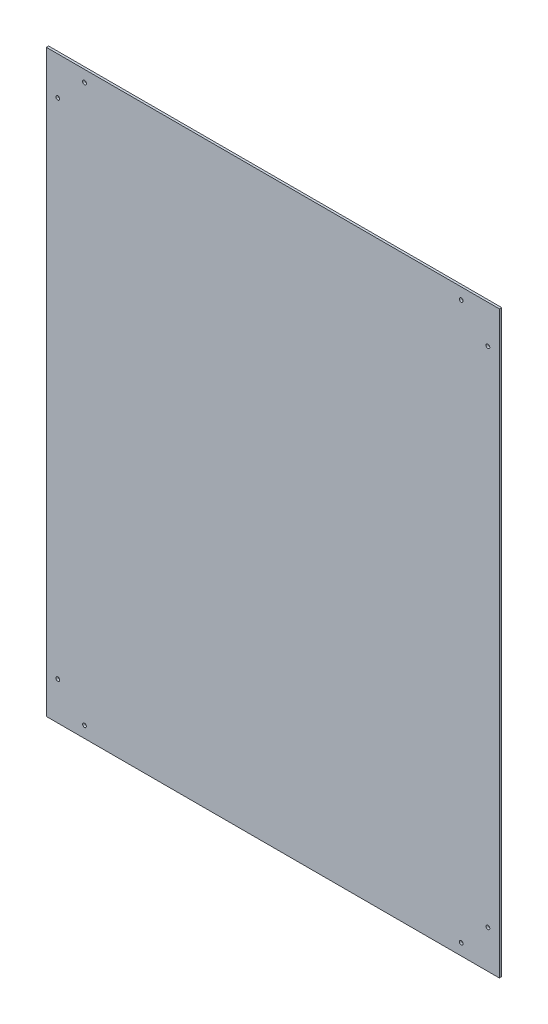
SolidWorks part; units mm, degrees
ref_plane "Plan de face" through (0, 0, 0) normal (0, 0, 1) x (1, 0, 0)
ref_plane "Plan de dessus" through (0, 0, 0) normal (0, 1, 0) x (1, 0, 0)
ref_plane "Plan de droite" through (0, 0, 0) normal (1, 0, 0) x (0, 0, -1)
sketch "Esquisse1" plane through (0, 0, 0) normal (0, 0, 1) x (1, 0, 0)
  line L1 (0, 0) -> (594, 0)
  line L2 (0, 0) -> (0, 760)
  line L3 (0, 760) -> (594, 760)
  line L4 (594, 0) -> (594, 760)
  dimension "D1" = 760
  dimension "D2" = 594
extrude "Boss.-Extru.1" add sketch "Esquisse1" along normal blind 3
sketch "Esquisse2" plane through (0, 0, 3) normal (0, 0, 1) x (1, 0, 0)
  line L0 (297, 760) -> (297, 0) construction
  line L1 (594, 760) -> (0, 760) construction
  line L2 (0, 0) -> (594, 0) construction
  line L3 (0, 760) -> (0, 0) construction
  circle A0 centre (50, 745) radius 2.5
  circle A1 centre (15, 710) radius 2.5
  circle A2 centre (15, 50) radius 2.5
  circle A3 centre (50, 15) radius 2.5
  circle A4 centre (544, 15) radius 2.5
  circle A5 centre (579, 50) radius 2.5
  circle A6 centre (579, 710) radius 2.5
  circle A7 centre (544, 745) radius 2.5
  dimension "D1" = 5
  dimension "D2" = 15
  dimension "D3" = 15
  dimension "D4" = 50
  dimension "D5" = 50
  dimension "D6" = 15
  dimension "D7" = 50
  dimension "D8" = 50
  dimension "D9" = 15
extrude "Enlèv. mat.-Extru.1" cut sketch "Esquisse2" against normal blind 3
